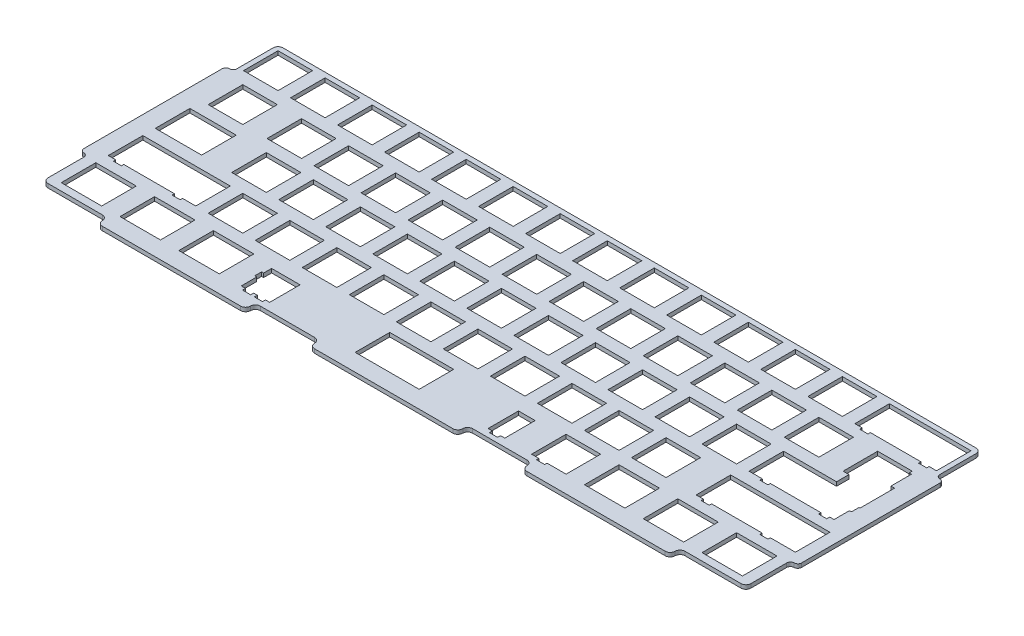
SolidWorks part; units mm, degrees
ref_plane "Front Plane" through (0, 0, 0) normal (0, 0, 1) x (1, 0, 0)
ref_plane "Top Plane" through (0, 0, 0) normal (0, 1, 0) x (1, 0, 0)
ref_plane "Right Plane" through (0, 0, 0) normal (1, 0, 0) x (0, 0, -1)
sketch "Sketch1" plane through (0, 0, 0) normal (0, 1, 0) x (1, 0, 0)
  line L0 (-17.7313, -28.9512) -> (-17.7313, -33.6517)
  line L1 (-52.5984, -33.6517) -> (-52.5984, -30.4215)
  line L2 (-52.5984, -30.4215) -> (-64.1063, -30.4215)
  line L3 (-64.1063, -30.4215) -> (-64.1063, -33.6517)
  line L4 (-64.1063, -33.6517) -> (-64.9304, -33.6517)
  line L5 (-64.9304, -33.6517) -> (-64.9304, -36.4505)
  line L6 (-64.9304, -36.4505) -> (-64.1063, -36.4505)
  line L7 (-64.1063, -36.4505) -> (-64.1063, -42.7205)
  line L8 (-64.1063, -42.7205) -> (-62.3813, -42.7205)
  line L9 (-62.3813, -42.7205) -> (-62.3813, -43.9208)
  line L10 (-62.3813, -43.9208) -> (-59.0807, -43.9208)
  line L11 (-59.0807, -43.9208) -> (-59.0807, -42.7205)
  line L12 (-59.0807, -42.7205) -> (-57.6241, -42.7205)
  line L13 (-57.6241, -42.7205) -> (-57.6241, -43.9208)
  line L14 (-57.6241, -43.9208) -> (-54.3238, -43.9208)
  line L15 (-54.3238, -43.9208) -> (-54.3238, -42.7205)
  line L16 (-54.3238, -42.7205) -> (-52.5984, -42.7205)
  line L17 (-52.5984, -42.7205) -> (-52.5984, -38.2516)
  line L18 (-17.7313, -33.6517) -> (-17.7313, -42.9507)
  line L19 (-17.7313, -42.9507) -> (8.1757, -42.9507)
  line L20 (8.1757, -42.9507) -> (8.1757, -38.2516)
  line L21 (35.8937, -33.6517) -> (35.8937, -42.7205)
  line L22 (35.8937, -42.7205) -> (37.6187, -42.7205)
  line L23 (37.6187, -42.7205) -> (37.6187, -43.9208)
  line L24 (37.6187, -43.9208) -> (40.9197, -43.9208)
  line L25 (40.9197, -43.9208) -> (40.9197, -42.7205)
  line L26 (40.9197, -42.7205) -> (42.6447, -42.7205)
  line L27 (42.6447, -42.7205) -> (42.6447, -38.2516)
  line L28 (53.7077, -38.2516) -> (53.7077, -42.9507)
  line L29 (53.7077, -42.9507) -> (56.6757, -42.9507)
  line L30 (56.6757, -42.9507) -> (56.6757, -43.9208)
  line L31 (56.6757, -43.9208) -> (59.9757, -43.9208)
  line L32 (59.9757, -43.9208) -> (59.9757, -42.9507)
  line L33 (59.9757, -42.9507) -> (67.7067, -42.9507)
  line L34 (67.7067, -42.9507) -> (67.7067, -28.9512)
  line L35 (67.7067, -28.9512) -> (53.7077, -28.9512)
  line L36 (53.7077, -28.9512) -> (53.7077, -33.6517)
  line L37 (42.6447, -33.6517) -> (42.6447, -30.4215)
  line L38 (42.6447, -30.4215) -> (35.8937, -30.4215)
  line L39 (35.8937, -30.4215) -> (35.8937, -33.6517)
  line L40 (8.1757, -33.6517) -> (8.1757, -28.9512)
  line L41 (8.1757, -28.9512) -> (-17.7313, -28.9512)
  line L42 (122.7637, -28.9512) -> (139.1447, -28.9512)
  line L43 (139.1447, -28.9512) -> (139.1447, -42.9507)
  line L44 (139.1447, -42.9507) -> (122.7637, -42.9507)
  line L45 (122.7637, -42.9507) -> (122.7637, -28.9512)
  line L46 (98.9517, -28.9512) -> (115.3317, -28.9512)
  line L47 (115.3317, -28.9512) -> (115.3317, -42.9507)
  line L48 (115.3317, -42.9507) -> (98.9517, -42.9507)
  line L49 (98.9517, -42.9507) -> (98.9517, -28.9512)
  line L50 (75.1387, -28.9512) -> (91.5197, -28.9512)
  line L51 (91.5197, -28.9512) -> (91.5197, -42.9507)
  line L52 (91.5197, -42.9507) -> (75.1387, -42.9507)
  line L53 (75.1387, -42.9507) -> (75.1387, -28.9512)
  line L54 (-89.1673, -28.9512) -> (-72.7868, -28.9512)
  line L55 (-72.7868, -28.9512) -> (-72.7868, -42.9507)
  line L56 (-72.7868, -42.9507) -> (-89.1673, -42.9507)
  line L57 (-89.1673, -42.9507) -> (-89.1673, -28.9512)
  line L58 (-112.9813, -28.9512) -> (-96.5993, -28.9512)
  line L59 (-96.5993, -28.9512) -> (-96.5993, -42.9507)
  line L60 (-96.5993, -42.9507) -> (-112.9813, -42.9507)
  line L61 (-112.9813, -42.9507) -> (-112.9813, -28.9512)
  line L62 (-136.7923, -28.9512) -> (-120.4116, -28.9512)
  line L63 (-120.4116, -28.9512) -> (-120.4116, -42.9507)
  line L64 (-120.4116, -42.9507) -> (-136.7923, -42.9507)
  line L65 (-136.7923, -42.9507) -> (-136.7923, -28.9512)
  line L66 (101.3327, -9.9013) -> (101.3327, -23.9007)
  line L67 (101.3327, -23.9007) -> (104.3077, -23.9007)
  line L68 (104.3077, -23.9007) -> (104.3077, -24.8708)
  line L69 (104.3077, -24.8708) -> (107.6067, -24.8708)
  line L70 (107.6067, -24.8708) -> (107.6067, -23.9007)
  line L71 (107.6067, -23.9007) -> (124.8567, -23.9007)
  line L72 (127.5267, -23.9007) -> (128.1067, -23.9007)
  line L73 (128.1067, -23.9007) -> (128.1067, -24.8708)
  line L74 (128.1067, -24.8708) -> (131.4067, -24.8708)
  line L75 (131.4067, -24.8708) -> (131.4067, -23.9007)
  line L76 (131.4067, -23.9007) -> (141.5257, -23.9007)
  line L77 (141.5257, -23.9007) -> (141.5257, -9.9013)
  line L78 (141.5257, -9.9013) -> (127.5267, -9.9013)
  line L79 (124.8567, -9.9013) -> (101.3327, -9.9013)
  line L80 (-136.7923, -9.9013) -> (-136.7923, -23.9007)
  line L81 (-136.7923, -23.9007) -> (-133.8172, -23.9007)
  line L82 (-133.8172, -23.9007) -> (-133.8172, -24.8708)
  line L83 (-133.8172, -24.8708) -> (-130.5182, -24.8708)
  line L84 (-130.5182, -24.8708) -> (-130.5182, -23.9007)
  line L85 (-130.5182, -23.9007) -> (-110.0185, -23.9007)
  line L86 (-110.0185, -23.9007) -> (-110.0185, -24.8708)
  line L87 (-110.0185, -24.8708) -> (-106.7181, -24.8708)
  line L88 (-106.7181, -24.8708) -> (-106.7181, -23.9007)
  line L89 (-106.7181, -23.9007) -> (-101.3618, -23.9007)
  line L90 (-101.3618, -23.9007) -> (-101.3618, -9.9013)
  line L91 (-101.3618, -9.9013) -> (-136.7923, -9.9013)
  line L92 (75.1387, -9.9013) -> (89.1387, -9.9013)
  line L93 (89.1387, -9.9013) -> (89.1387, -23.9007)
  line L94 (89.1387, -23.9007) -> (75.1387, -23.9007)
  line L95 (75.1387, -23.9007) -> (75.1387, -9.9013)
  line L96 (56.0887, -9.9013) -> (70.0887, -9.9013)
  line L97 (70.0887, -9.9013) -> (70.0887, -23.9007)
  line L98 (70.0887, -23.9007) -> (56.0887, -23.9007)
  line L99 (56.0887, -23.9007) -> (56.0887, -9.9013)
  line L100 (37.0387, -9.9013) -> (51.0387, -9.9013)
  line L101 (51.0387, -9.9013) -> (51.0387, -23.9007)
  line L102 (51.0387, -23.9007) -> (37.0387, -23.9007)
  line L103 (37.0387, -23.9007) -> (37.0387, -9.9013)
  line L104 (17.9887, -9.9013) -> (31.9887, -9.9013)
  line L105 (31.9887, -9.9013) -> (31.9887, -23.9007)
  line L106 (31.9887, -23.9007) -> (17.9887, -23.9007)
  line L107 (17.9887, -23.9007) -> (17.9887, -9.9013)
  line L108 (-1.0613, -9.9013) -> (12.9387, -9.9013)
  line L109 (12.9387, -9.9013) -> (12.9387, -23.9007)
  line L110 (12.9387, -23.9007) -> (-1.0613, -23.9007)
  line L111 (-1.0613, -23.9007) -> (-1.0613, -9.9013)
  line L112 (-20.1113, -9.9013) -> (-6.1113, -9.9013)
  line L113 (-6.1113, -9.9013) -> (-6.1113, -23.9007)
  line L114 (-6.1113, -23.9007) -> (-20.1113, -23.9007)
  line L115 (-20.1113, -23.9007) -> (-20.1113, -9.9013)
  line L116 (-39.1613, -9.9013) -> (-25.1613, -9.9013)
  line L117 (-25.1613, -9.9013) -> (-25.1613, -23.9007)
  line L118 (-25.1613, -23.9007) -> (-39.1613, -23.9007)
  line L119 (-39.1613, -23.9007) -> (-39.1613, -9.9013)
  line L120 (-58.2111, -9.9013) -> (-44.2118, -9.9013)
  line L121 (-44.2118, -9.9013) -> (-44.2118, -23.9007)
  line L122 (-44.2118, -23.9007) -> (-58.2111, -23.9007)
  line L123 (-58.2111, -23.9007) -> (-58.2111, -9.9013)
  line L124 (-77.2611, -9.9013) -> (-63.2618, -9.9013)
  line L125 (-63.2618, -9.9013) -> (-63.2618, -23.9007)
  line L126 (-63.2618, -23.9007) -> (-77.2611, -23.9007)
  line L127 (-77.2611, -23.9007) -> (-77.2611, -9.9013)
  line L128 (-96.3111, -9.9013) -> (-82.3118, -9.9013)
  line L129 (-82.3118, -9.9013) -> (-82.3118, -23.9007)
  line L130 (-82.3118, -23.9007) -> (-96.3111, -23.9007)
  line L131 (-96.3111, -23.9007) -> (-96.3111, -9.9013)
  line L132 (122.7637, 28.1988) -> (122.7637, 14.1995)
  line L133 (122.7637, 14.1995) -> (125.1437, 14.1995)
  line L134 (125.1437, 14.1995) -> (125.1437, 9.1488)
  line L135 (125.1437, 9.1488) -> (103.7137, 9.1488)
  line L136 (103.7137, 9.1488) -> (103.7137, -4.8505)
  line L137 (103.7137, -4.8505) -> (109.0687, -4.8505)
  line L138 (109.0687, -4.8505) -> (109.0687, -5.8207)
  line L139 (109.0687, -5.8207) -> (112.3677, -5.8207)
  line L140 (112.3677, -5.8207) -> (112.3677, -4.8505)
  line L141 (112.3677, -4.8505) -> (129.6197, -4.8505)
  line L142 (132.8687, -5.8207) -> (136.1697, -5.8207)
  line L143 (136.1697, -5.8207) -> (136.1697, -4.6205)
  line L144 (136.1697, -4.6205) -> (137.8947, -4.6205)
  line L145 (137.8947, -4.6205) -> (137.8947, 1.6494)
  line L146 (137.8947, 1.6494) -> (138.7187, 1.6494)
  line L147 (138.7187, 1.6494) -> (138.7187, 4.4483)
  line L148 (139.1447, 4.6745) -> (139.1447, 18.6738)
  line L149 (137.6737, 20.1992) -> (137.6737, 26.9489)
  line L150 (137.6737, 26.9489) -> (136.7637, 26.9489)
  line L151 (136.7637, 26.9489) -> (136.7637, 28.1988)
  line L152 (136.7637, 28.1988) -> (122.7637, 28.1988)
  line L153 (84.6637, 9.1488) -> (98.6637, 9.1488)
  line L154 (98.6637, 9.1488) -> (98.6637, -4.8505)
  line L155 (98.6637, -4.8505) -> (84.6637, -4.8505)
  line L156 (84.6637, -4.8505) -> (84.6637, 9.1488)
  line L157 (65.6137, 9.1488) -> (79.6137, 9.1488)
  line L158 (79.6137, 9.1488) -> (79.6137, -4.8505)
  line L159 (79.6137, -4.8505) -> (65.6137, -4.8505)
  line L160 (65.6137, -4.8505) -> (65.6137, 9.1488)
  line L161 (46.5637, 9.1488) -> (60.5637, 9.1488)
  line L162 (60.5637, 9.1488) -> (60.5637, -4.8505)
  line L163 (60.5637, -4.8505) -> (46.5637, -4.8505)
  line L164 (46.5637, -4.8505) -> (46.5637, 9.1488)
  line L165 (27.5137, 9.1488) -> (41.5137, 9.1488)
  line L166 (41.5137, 9.1488) -> (41.5137, -4.8505)
  line L167 (41.5137, -4.8505) -> (27.5137, -4.8505)
  line L168 (27.5137, -4.8505) -> (27.5137, 9.1488)
  line L169 (8.4637, 9.1488) -> (22.4637, 9.1488)
  line L170 (22.4637, 9.1488) -> (22.4637, -4.8505)
  line L171 (22.4637, -4.8505) -> (8.4637, -4.8505)
  line L172 (8.4637, -4.8505) -> (8.4637, 9.1488)
  line L173 (-10.5863, 9.1488) -> (3.4137, 9.1488)
  line L174 (3.4137, 9.1488) -> (3.4137, -4.8505)
  line L175 (3.4137, -4.8505) -> (-10.5863, -4.8505)
  line L176 (-10.5863, -4.8505) -> (-10.5863, 9.1488)
  line L177 (-29.6363, 9.1488) -> (-15.6363, 9.1488)
  line L178 (-15.6363, 9.1488) -> (-15.6363, -4.8505)
  line L179 (-15.6363, -4.8505) -> (-29.6363, -4.8505)
  line L180 (-29.6363, -4.8505) -> (-29.6363, 9.1488)
  line L181 (-48.6861, 9.1488) -> (-34.6863, 9.1488)
  line L182 (-34.6863, 9.1488) -> (-34.6863, -4.8505)
  line L183 (-34.6863, -4.8505) -> (-48.6861, -4.8505)
  line L184 (-48.6861, -4.8505) -> (-48.6861, 9.1488)
  line L185 (-67.7361, 9.1488) -> (-53.7368, 9.1488)
  line L186 (-53.7368, 9.1488) -> (-53.7368, -4.8505)
  line L187 (-53.7368, -4.8505) -> (-67.7361, -4.8505)
  line L188 (-67.7361, -4.8505) -> (-67.7361, 9.1488)
  line L189 (-86.7861, 9.1488) -> (-72.7868, 9.1488)
  line L190 (-72.7868, 9.1488) -> (-72.7868, -4.8505)
  line L191 (-72.7868, -4.8505) -> (-86.7861, -4.8505)
  line L192 (-86.7861, -4.8505) -> (-86.7861, 9.1488)
  line L193 (-105.8361, 9.1488) -> (-91.8368, 9.1488)
  line L194 (-91.8368, 9.1488) -> (-91.8368, -4.8505)
  line L195 (-91.8368, -4.8505) -> (-105.8361, -4.8505)
  line L196 (-105.8361, -4.8505) -> (-105.8361, 9.1488)
  line L197 (-136.7923, 9.1488) -> (-118.0304, 9.1488)
  line L198 (-118.0304, 9.1488) -> (-118.0304, -4.8505)
  line L199 (-118.0304, -4.8505) -> (-136.7923, -4.8505)
  line L200 (-136.7923, -4.8505) -> (-136.7923, 9.1488)
  line L201 (98.9517, 28.1988) -> (112.9507, 28.1988)
  line L202 (112.9507, 28.1988) -> (112.9507, 14.1995)
  line L203 (112.9507, 14.1995) -> (98.9517, 14.1995)
  line L204 (98.9517, 14.1995) -> (98.9517, 28.1988)
  line L205 (79.9017, 28.1988) -> (93.9007, 28.1988)
  line L206 (93.9007, 28.1988) -> (93.9007, 14.1995)
  line L207 (93.9007, 14.1995) -> (79.9017, 14.1995)
  line L208 (79.9017, 14.1995) -> (79.9017, 28.1988)
  line L209 (60.8517, 28.1988) -> (74.8507, 28.1988)
  line L210 (74.8507, 28.1988) -> (74.8507, 14.1995)
  line L211 (74.8507, 14.1995) -> (60.8517, 14.1995)
  line L212 (60.8517, 14.1995) -> (60.8517, 28.1988)
  line L213 (41.8017, 28.1988) -> (55.8007, 28.1988)
  line L214 (55.8007, 28.1988) -> (55.8007, 14.1995)
  line L215 (55.8007, 14.1995) -> (41.8017, 14.1995)
  line L216 (41.8017, 14.1995) -> (41.8017, 28.1988)
  line L217 (22.7517, 28.1988) -> (36.7507, 28.1988)
  line L218 (36.7507, 28.1988) -> (36.7507, 14.1995)
  line L219 (36.7507, 14.1995) -> (22.7517, 14.1995)
  line L220 (22.7517, 14.1995) -> (22.7517, 28.1988)
  line L221 (3.7017, 28.1988) -> (17.7007, 28.1988)
  line L222 (17.7007, 28.1988) -> (17.7007, 14.1995)
  line L223 (17.7007, 14.1995) -> (3.7017, 14.1995)
  line L224 (3.7017, 14.1995) -> (3.7017, 28.1988)
  line L225 (-15.3483, 28.1988) -> (-1.3493, 28.1988)
  line L226 (-1.3493, 28.1988) -> (-1.3493, 14.1995)
  line L227 (-1.3493, 14.1995) -> (-15.3483, 14.1995)
  line L228 (-15.3483, 14.1995) -> (-15.3483, 28.1988)
  line L229 (-34.3983, 28.1988) -> (-20.3993, 28.1988)
  line L230 (-20.3993, 28.1988) -> (-20.3993, 14.1995)
  line L231 (-20.3993, 14.1995) -> (-34.3983, 14.1995)
  line L232 (-34.3983, 14.1995) -> (-34.3983, 28.1988)
  line L233 (-53.4486, 28.1988) -> (-39.4493, 28.1988)
  line L234 (-39.4493, 28.1988) -> (-39.4493, 14.1995)
  line L235 (-39.4493, 14.1995) -> (-53.4486, 14.1995)
  line L236 (-53.4486, 14.1995) -> (-53.4486, 28.1988)
  line L237 (-72.4986, 28.1988) -> (-58.4993, 28.1988)
  line L238 (-58.4993, 28.1988) -> (-58.4993, 14.1995)
  line L239 (-58.4993, 14.1995) -> (-72.4986, 14.1995)
  line L240 (-72.4986, 14.1995) -> (-72.4986, 28.1988)
  line L241 (-91.5486, 28.1988) -> (-77.5493, 28.1988)
  line L242 (-77.5493, 28.1988) -> (-77.5493, 14.1995)
  line L243 (-77.5493, 14.1995) -> (-91.5486, 14.1995)
  line L244 (-91.5486, 14.1995) -> (-91.5486, 28.1988)
  line L245 (-110.5986, 28.1988) -> (-96.5993, 28.1988)
  line L246 (-96.5993, 28.1988) -> (-96.5993, 14.1995)
  line L247 (-96.5993, 14.1995) -> (-110.5986, 14.1995)
  line L248 (-110.5986, 14.1995) -> (-110.5986, 28.1988)
  line L249 (-134.4111, 28.1988) -> (-120.4116, 28.1988)
  line L250 (-120.4116, 28.1988) -> (-120.4116, 14.1995)
  line L251 (-120.4116, 14.1995) -> (-134.4111, 14.1995)
  line L252 (-134.4111, 14.1995) -> (-134.4111, 28.1988)
  line L253 (108.4767, 47.2488) -> (108.4767, 33.2495)
  line L254 (108.4767, 33.2495) -> (111.4497, 33.2495)
  line L255 (111.4497, 33.2495) -> (111.4497, 32.2793)
  line L256 (111.4497, 32.2793) -> (114.7507, 32.2793)
  line L257 (114.7507, 32.2793) -> (114.7507, 33.2495)
  line L258 (114.7507, 33.2495) -> (135.2517, 33.2495)
  line L259 (135.2517, 33.2495) -> (135.2517, 32.2793)
  line L260 (135.2517, 32.2793) -> (138.5507, 32.2793)
  line L261 (138.5507, 32.2793) -> (138.5507, 33.2495)
  line L262 (138.5507, 33.2495) -> (141.5257, 33.2495)
  line L263 (141.5257, 33.2495) -> (141.5257, 47.2488)
  line L264 (141.5257, 47.2488) -> (108.4767, 47.2488)
  line L265 (89.4267, 47.2488) -> (103.4257, 47.2488)
  line L266 (103.4257, 47.2488) -> (103.4257, 33.2495)
  line L267 (103.4257, 33.2495) -> (89.4267, 33.2495)
  line L268 (89.4267, 33.2495) -> (89.4267, 47.2488)
  line L269 (70.3767, 47.2488) -> (84.3757, 47.2488)
  line L270 (84.3757, 47.2488) -> (84.3757, 33.2495)
  line L271 (84.3757, 33.2495) -> (70.3767, 33.2495)
  line L272 (70.3767, 33.2495) -> (70.3767, 47.2488)
  line L273 (51.3267, 47.2488) -> (65.3257, 47.2488)
  line L274 (65.3257, 47.2488) -> (65.3257, 33.2495)
  line L275 (65.3257, 33.2495) -> (51.3267, 33.2495)
  line L276 (51.3267, 33.2495) -> (51.3267, 47.2488)
  line L277 (32.2767, 47.2488) -> (46.2757, 47.2488)
  line L278 (46.2757, 47.2488) -> (46.2757, 33.2495)
  line L279 (46.2757, 33.2495) -> (32.2767, 33.2495)
  line L280 (32.2767, 33.2495) -> (32.2767, 47.2488)
  line L281 (13.2267, 47.2488) -> (27.2257, 47.2488)
  line L282 (27.2257, 47.2488) -> (27.2257, 33.2495)
  line L283 (27.2257, 33.2495) -> (13.2267, 33.2495)
  line L284 (13.2267, 33.2495) -> (13.2267, 47.2488)
  line L285 (-5.8233, 47.2488) -> (8.1757, 47.2488)
  line L286 (8.1757, 47.2488) -> (8.1757, 33.2495)
  line L287 (8.1757, 33.2495) -> (-5.8233, 33.2495)
  line L288 (-5.8233, 33.2495) -> (-5.8233, 47.2488)
  line L289 (-24.8753, 47.2488) -> (-10.8743, 47.2488)
  line L290 (-10.8743, 47.2488) -> (-10.8743, 33.2495)
  line L291 (-10.8743, 33.2495) -> (-24.8753, 33.2495)
  line L292 (-24.8753, 33.2495) -> (-24.8753, 47.2488)
  line L293 (-43.925, 47.2488) -> (-29.9243, 47.2488)
  line L294 (-29.9243, 47.2488) -> (-29.9243, 33.2495)
  line L295 (-29.9243, 33.2495) -> (-43.925, 33.2495)
  line L296 (-43.925, 33.2495) -> (-43.925, 47.2488)
  line L297 (-62.9736, 47.2488) -> (-48.9743, 47.2488)
  line L298 (-48.9743, 47.2488) -> (-48.9743, 33.2495)
  line L299 (-48.9743, 33.2495) -> (-62.9736, 33.2495)
  line L300 (-62.9736, 33.2495) -> (-62.9736, 47.2488)
  line L301 (-82.0236, 47.2488) -> (-68.0243, 47.2488)
  line L302 (-68.0243, 47.2488) -> (-68.0243, 33.2495)
  line L303 (-68.0243, 33.2495) -> (-82.0236, 33.2495)
  line L304 (-82.0236, 33.2495) -> (-82.0236, 47.2488)
  line L305 (-101.0736, 47.2488) -> (-87.0743, 47.2488)
  line L306 (-87.0743, 47.2488) -> (-87.0743, 33.2495)
  line L307 (-87.0743, 33.2495) -> (-101.0736, 33.2495)
  line L308 (-101.0736, 33.2495) -> (-101.0736, 47.2488)
  line L309 (-120.1236, 47.2488) -> (-106.1243, 47.2488)
  line L310 (-106.1243, 47.2488) -> (-106.1243, 33.2495)
  line L311 (-106.1243, 33.2495) -> (-120.1236, 33.2495)
  line L312 (-120.1236, 33.2495) -> (-120.1236, 47.2488)
  line L313 (-139.1736, 47.2488) -> (-125.1741, 47.2488)
  line L314 (-125.1741, 47.2488) -> (-125.1741, 33.2495)
  line L315 (-125.1741, 33.2495) -> (-139.1736, 33.2495)
  line L316 (-139.1736, 33.2495) -> (-139.1736, 47.2488)
  line L318 (53.7077, -38.2516) -> (53.7077, -33.6517)
  line L319 (42.6447, -38.2516) -> (42.6447, -33.6517)
  line L321 (8.1757, -38.2516) -> (8.1757, -33.6517)
  line L323 (-52.5984, -38.2516) -> (-52.5984, -33.6517)
  line L324 (124.8567, -9.9013) -> (127.5267, -9.9013)
  line L325 (124.8567, -23.9007) -> (127.5267, -23.9007)
  line L326 (138.7187, 4.4483) -> (138.7187, 4.6745)
  line L327 (138.7187, 4.6745) -> (139.1447, 4.6745)
  line L328 (137.6737, 20.1992) -> (137.6737, 18.6738)
  line L329 (137.6737, 18.6738) -> (139.1447, 18.6738)
  line L330 (129.6197, -4.8505) -> (132.8687, -4.8505)
  line L331 (132.8687, -4.8505) -> (132.8687, -5.8207)
  line L332 (-113.1736, -49.9208) -> (-57.1736, -49.9208)
  line L333 (-53.1736, -45.9208) -> (-31.1736, -45.9208)
  line L334 (-27.1736, -49.9208) -> (28.8264, -49.9208)
  line L335 (32.8264, -45.9208) -> (54.8264, -45.9208)
  line L336 (58.8264, -49.9208) -> (114.8264, -49.9208)
  line L337 (146.5257, -26.4208) -> (146.5257, 29.5792)
  line L338 (-144.1736, -26.4208) -> (-144.1736, 29.5792)
  line L339 (-141.1736, 32.5792) -> (-141.1736, 47.2488)
  line L340 (-139.1736, 49.2488) -> (141.5257, 49.2488)
  line L341 (143.5257, 32.5792) -> (143.5257, 47.2488)
  line L342 (118.8264, -45.9208) -> (141.5257, -45.9208)
  line L343 (143.5257, -43.9208) -> (143.5257, -29.4208)
  line L344 (-139.1736, -45.9208) -> (-117.1736, -45.9208)
  line L345 (-141.1736, -43.9208) -> (-141.1736, -29.4208)
  arc A0 (-115.1736, -47.9208) -> (-113.1736, -49.9208) centre (-113.1736, -47.9208) ccw
  arc A1 (-115.1736, -47.9208) -> (-117.1736, -45.9208) centre (-117.1736, -47.9208) ccw
  arc A2 (-57.1736, -49.9208) -> (-55.1736, -47.9208) centre (-57.1736, -47.9208) ccw
  arc A3 (-53.1736, -45.9208) -> (-55.1736, -47.9208) centre (-53.1736, -47.9208) ccw
  arc A4 (-29.1736, -47.9208) -> (-27.1736, -49.9208) centre (-27.1736, -47.9208) ccw
  arc A5 (-29.1736, -47.9208) -> (-31.1736, -45.9208) centre (-31.1736, -47.9208) ccw
  arc A6 (28.8264, -49.9208) -> (30.8264, -47.9208) centre (28.8264, -47.9208) ccw
  arc A7 (32.8264, -45.9208) -> (30.8264, -47.9208) centre (32.8264, -47.9208) ccw
  arc A8 (56.8264, -47.9208) -> (54.8264, -45.9208) centre (54.8264, -47.9208) ccw
  arc A9 (56.8264, -47.9208) -> (58.8264, -49.9208) centre (58.8264, -47.9208) ccw
  arc A10 (114.8264, -49.9208) -> (116.8264, -47.9208) centre (114.8264, -47.9208) ccw
  arc A11 (118.8264, -45.9208) -> (116.8264, -47.9208) centre (118.8264, -47.9208) ccw
  arc A12 (145.0257, -27.9208) -> (146.5257, -26.4208) centre (145.0257, -26.4208) ccw
  arc A13 (145.0257, -27.9208) -> (143.5257, -29.4208) centre (145.0257, -29.4208) ccw
  arc A14 (146.5257, 29.5792) -> (145.0257, 31.0792) centre (145.0257, 29.5792) ccw
  arc A15 (143.5257, 32.5792) -> (145.0257, 31.0792) centre (145.0257, 32.5792) ccw
  arc A16 (-141.1736, -29.4208) -> (-142.6736, -27.9208) centre (-142.6736, -29.4208) ccw
  arc A17 (-144.1736, -26.4208) -> (-142.6736, -27.9208) centre (-142.6736, -26.4208) ccw
  arc A18 (-142.6736, 31.0792) -> (-144.1736, 29.5792) centre (-142.6736, 29.5792) ccw
  arc A19 (-142.6736, 31.0792) -> (-141.1736, 32.5792) centre (-142.6736, 32.5792) ccw
  arc A20 (-139.1736, 49.2488) -> (-141.1736, 47.2488) centre (-139.1736, 47.2488) ccw
  arc A21 (143.5257, 47.2488) -> (141.5257, 49.2488) centre (141.5257, 47.2488) ccw
  arc A22 (141.5257, -45.9208) -> (143.5257, -43.9208) centre (141.5257, -43.9208) ccw
  arc A23 (-141.1736, -43.9208) -> (-139.1736, -45.9208) centre (-139.1736, -43.9208) ccw
extrude "Boss-Extrude2" add sketch "Sketch1" along normal blind 1.6
